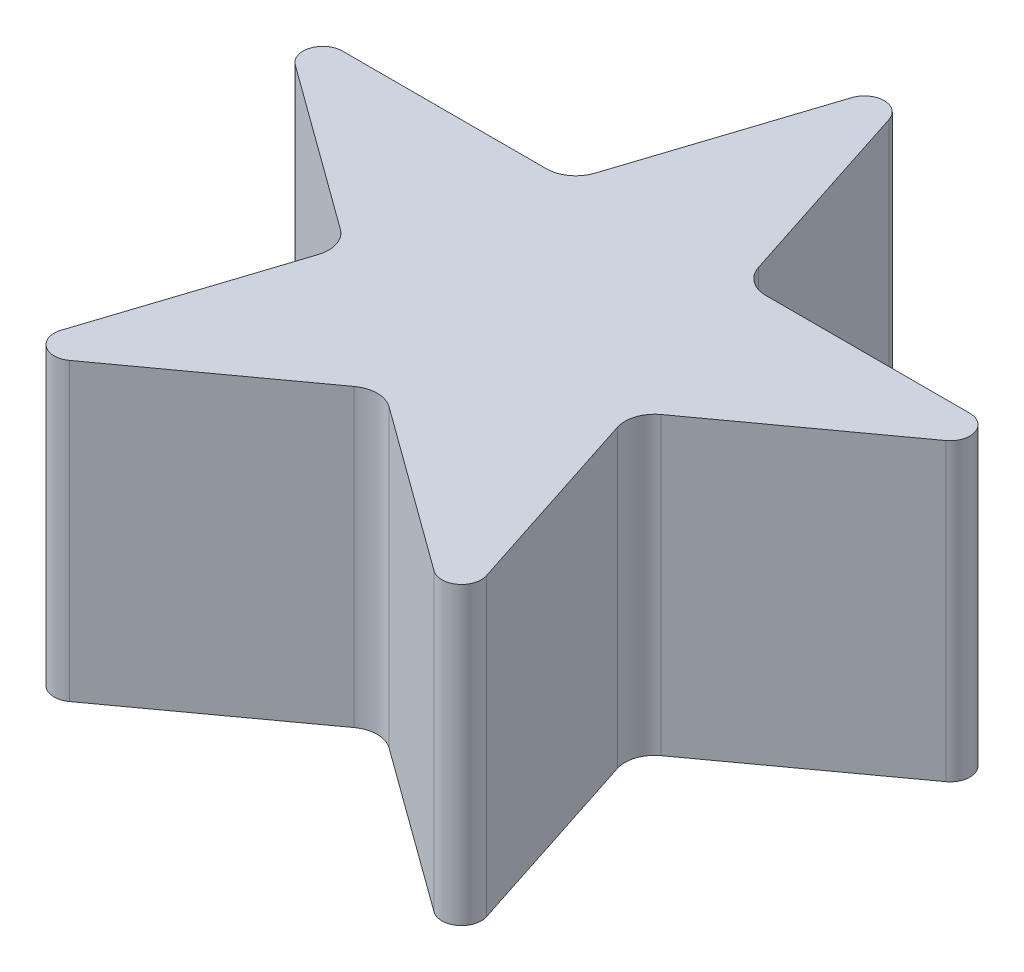
SolidWorks part; units mm, degrees
ref_plane "Front Plane" through (0, 0, 0) normal (0, 0, 1) x (1, 0, 0)
ref_plane "Top Plane" through (0, 0, 0) normal (0, 1, 0) x (1, 0, 0)
ref_plane "Right Plane" through (0, 0, 0) normal (1, 0, 0) x (0, 0, -1)
sketch "Sketch2" plane through (0, 0, 0) normal (0, 1, 0) x (1, 0, 0)
  line L16 (0, 39.9623) -> (-23.4892, -32.3302)
  line L17 (0, 39.9623) -> (23.4892, -32.3302)
  line L18 (38.0064, 12.349) -> (-38.0064, 12.349)
  line L19 (38.0064, 12.349) -> (-23.4892, -32.3302)
  line L20 (23.4892, -32.3302) -> (-38.0064, 12.349)
extrude "Boss-Extrude1" add sketch "Sketch2" along normal blind 30 contours L19 L18 L17 | L20 L19 L17 L18 L16 | L20 L17 L19 | L19 L20 L16 | L20 L16 L18 | L18 L17 L16
fillet "Fillet1" radius 2 5 edges at (23.4892, 15, 32.3302) (38.0064, 15, -12.349) (-23.4892, 15, 32.3302) (-38.0064, 15, -12.349) (0, 15, -39.9623)
fillet "Fillet2" radius 3 5 edges at (-8.9721, 15, -12.349) (-14.5171, 15, 4.7169) (0, 15, 15.2642) (14.5171, 15, 4.7169) (8.9721, 15, -12.349)
